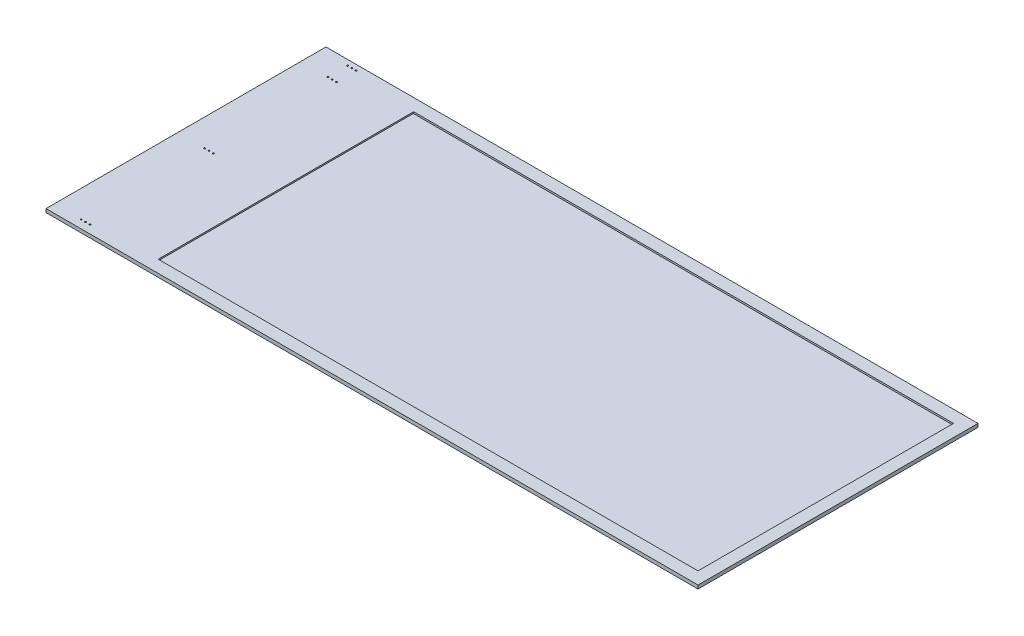
SolidWorks part; units mm, degrees
material "Pine"
ref_plane "Front Plane" through (0, 0, 0) normal (0, 0, 1) x (1, 0, 0)
ref_plane "Top Plane" through (0, 0, 0) normal (0, 1, 0) x (1, 0, 0)
ref_plane "Right Plane" through (0, 0, 0) normal (1, 0, 0) x (0, 0, -1)
sketch "Sketch1" plane through (0, 0, 0) normal (0, 1, 0) x (1, 0, 0)
  line L1 (0, 0) -> (1066.8, 0)
  line L2 (0, 0) -> (0, 508)
  line L3 (0, 508) -> (1066.8, 508)
  line L4 (1066.8, 0) -> (1066.8, 508)
  dimension "D1" = 1066.8
  dimension "D2" = 508
extrude "Boss-Extrude1" add sketch "Sketch1" along normal blind 6.35
sketch "Sketch2" plane through (0, 6.35, 0) normal (0, 1, 0) x (1, 0, 0)
  line L1 (125.4125, 485.775) -> (1044.575, 485.775)
  line L2 (125.4125, 485.775) -> (125.4125, 22.225)
  line L3 (125.4125, 22.225) -> (1044.575, 22.225)
  line L4 (1044.575, 485.775) -> (1044.575, 22.225)
  line L5 (0, 254) -> (1066.8, 254) construction
  line L6 (0, 508) -> (0, 0) construction
  line L7 (1066.8, 0) -> (1066.8, 508) construction
  point P10 (125.4125, 254)
  dimension "D1" = 919.1625
  dimension "D2" = 463.55
  dimension "D3" = 22.225
extrude "Cut-Extrude1" cut sketch "Sketch2" against normal blind 3.175
sketch "Sketch3" plane through (0, 6.35, 0) normal (0, 1, 0) x (1, 0, 0)
  line L0 (49.149, 462.4832) -> (49.149, -139.6835) construction
  line L1 (1044.575, 22.225) -> (1044.575, 485.775) construction
  line L2 (0, 508) -> (0, 0) construction
  line L3 (49.149, 498.094) -> (49.149, 508) construction
  line L4 (1066.8, 508) -> (0, 508) construction
  line L5 (1066.8, 0) -> (1066.8, 508) construction
  circle A0 centre (49.149, 462.4832) radius 1.3589
  circle A1 centre (49.149, 498.094) radius 1.3589
  circle A2 centre (56.8452, 498.094) radius 1.3589
  circle A3 centre (56.8452, 462.4832) radius 1.3589
  circle A4 centre (64.5414, 498.094) radius 1.3589
  circle A5 centre (64.5414, 462.4832) radius 1.3589
  circle A9 centre (49.149, 14.8082) radius 1.3589
  circle A10 centre (57.0992, 14.8082) radius 1.3589
  circle A11 centre (65.0494, 14.8082) radius 1.3589
  circle A12 centre (49.149, 238.6457) radius 1.3589
  circle A13 centre (57.0992, 238.6457) radius 1.3589
  circle A14 centre (65.0494, 238.6457) radius 1.3589
  dimension "D2" = 2.7178
  dimension "D3" = 2.7178
  dimension "D9" = 2.7178
  dimension "D5" = 9.906
  dimension "D1" = 35.6108
  dimension "D6" = 995.426
  dimension "D7" = 7.6962
  dimension "D8" = 49.149
  dimension "D10" = 447.675
  dimension "D11" = 7.9502
  dimension "D13" = 223.8375
  dimension "D4" = 3
  dimension "D12" = 3
extrude "Cut-Extrude2" cut sketch "Sketch3" against normal through all
sketch "Sketch5" plane through (0, 6.35, 0) normal (0, 1, 0) x (1, 0, 0)
  line L0 (1044.575, 22.225) -> (1044.575, 485.775) construction
  line L1 (125.4125, 22.225) -> (1044.575, 22.225) construction
  line L2 (125.4125, 485.775) -> (125.4125, 22.225) construction
  line L3 (1044.575, 485.775) -> (125.4125, 485.775) construction
  line L4 (1044.575, 22.225) -> (1044.575, 485.775)
  line L5 (125.4125, 22.225) -> (1044.575, 22.225)
  line L6 (125.4125, 485.775) -> (125.4125, 22.225)
  line L7 (1044.575, 485.775) -> (125.4125, 485.775)
  line L8 (181.3306, 22.225) -> (181.3306, 485.775)
  circle A1 centre (65.0494, 14.8082) radius 1.3589 construction
  point P8 (181.3306, 485.775)
  line M19 (125.4125, 22.225) -> (125.4125, 485.775)
  line M20 (125.4125, 485.775) -> (1044.575, 485.775)
  dimension "D1" = 116.2812
extrude "Boss-Extrude2" add sketch "Sketch5" against normal blind 2.54 contours L5 L8 M20 M19
sketch "Sketch6" plane through (0, 6.35, 0) normal (0, 1, 0) x (1, 0, 0)
  line L1 (1066.8, 508) -> (1183.0812, 508)
  line L2 (1066.8, 508) -> (1066.8, 0)
  line L3 (1066.8, 0) -> (1183.0812, 0)
  line L4 (1183.0812, 508) -> (1183.0812, 0)
  dimension "D1" = 116.2812
extrude "Boss-Extrude3" add sketch "Sketch6" against normal blind 6.35
sketch "Sketch7" plane through (0, 6.35, 0) normal (0, 1, 0) x (1, 0, 0)
  line L1 (1044.575, 485.775) -> (1160.8562, 485.775)
  line L2 (1044.575, 485.775) -> (1044.575, 22.225)
  line L3 (1044.575, 22.225) -> (1160.8562, 22.225)
  line L4 (1160.8562, 485.775) -> (1160.8562, 22.225)
  dimension "D1" = 116.2812
extrude "Cut-Extrude3" cut sketch "Sketch7" against normal blind 3.175
